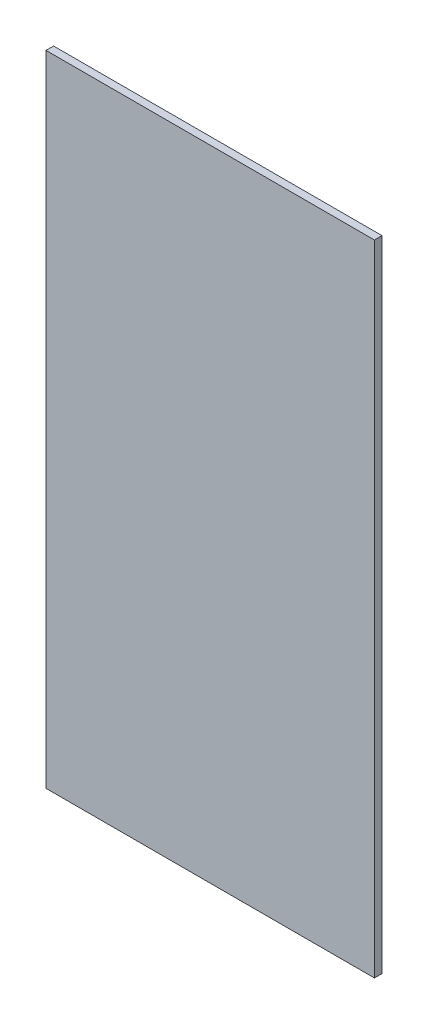
SolidWorks part; units mm, degrees
ref_plane "Front" through (0, 0, 0) normal (0, 0, 1) x (1, 0, 0)
ref_plane "Top" through (0, 0, 0) normal (0, 1, 0) x (1, 0, 0)
ref_plane "Right" through (0, 0, 0) normal (1, 0, 0) x (0, 0, -1)
sketch "Sketch1" plane through (0, 0, 0) normal (0, 0, 1) x (1, 0, 0)
  line L1 (0, 0) -> (260, 0)
  line L2 (0, 0) -> (0, 506)
  line L3 (0, 506) -> (260, 506)
  line L4 (260, 0) -> (260, 506)
  dimension "D1" = 260
  dimension "D2" = 506
extrude "Boss-Extrude1" add sketch "Sketch1" along normal blind 6
